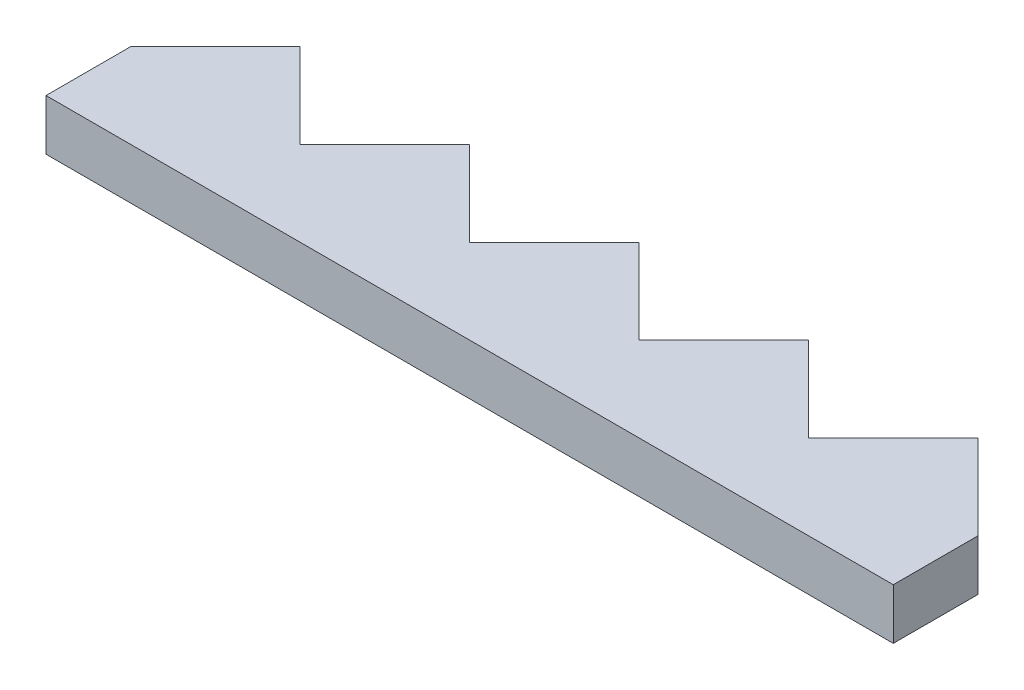
SolidWorks part; units mm, degrees
ref_plane "Front Plane" through (0, 0, 0) normal (0, 0, 1) x (1, 0, 0)
ref_plane "Top Plane" through (0, 0, 0) normal (0, 1, 0) x (1, 0, 0)
ref_plane "Right Plane" through (0, 0, 0) normal (1, 0, 0) x (0, 0, -1)
sketch "Sketch1" plane through (0, 0, 0) normal (0, 1, 0) x (1, 0, 0)
  line L0 (0, 5) -> (5, 10)
  line L2 (0, 5) -> (0, 0)
  line L3 (0, 0) -> (50, 0)
  line L5 (5, 10) -> (10, 5)
  line L6 (10, 5) -> (15, 10)
  line L7 (15, 10) -> (20, 5)
  line L8 (20, 5) -> (25, 10)
  line L9 (25, 10) -> (30, 5)
  line L10 (30, 5) -> (35, 10)
  line L11 (35, 10) -> (40, 5)
  line L12 (40, 5) -> (45, 10)
  line L13 (45, 10) -> (50, 5)
  line L18 (5, 10) -> (65, 10) construction
  line L19 (50, 5) -> (50, 0)
  point P4 (50.8643, 5)
  dimension "D1" = 5
  dimension "D2" = 10
  dimension "D4" = 10
  dimension "D5" = 5
extrude "Boss-Extrude1" add sketch "Sketch1" along normal blind 3
